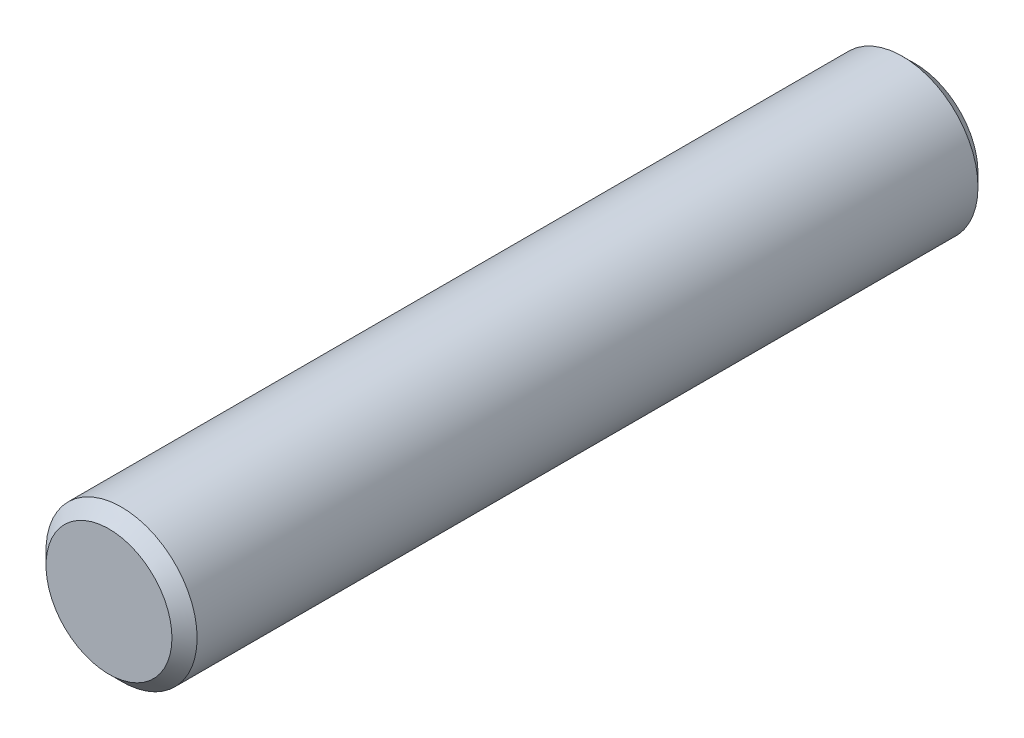
SolidWorks part; units mm, degrees
ref_plane "前基準面" through (0, 0, 0) normal (0, 0, 1) x (1, 0, 0)
ref_plane "上基準面" through (0, 0, 0) normal (0, 1, 0) x (1, 0, 0)
ref_plane "右基準面" through (0, 0, 0) normal (1, 0, 0) x (0, 0, -1)
sketch "草圖1" plane through (0, 0, 0) normal (0, 0, 1) x (1, 0, 0)
  circle A0 centre (0, 0) radius 3
extrude "填料-伸長1" add sketch "草圖1" along normal blind 32
chamfer "導角1" distance 0.5 angle 45 1 edges at (3, 0, 32)
chamfer "導角2" distance 0.5 angle 45 1 edges at (3, 0, 0)
